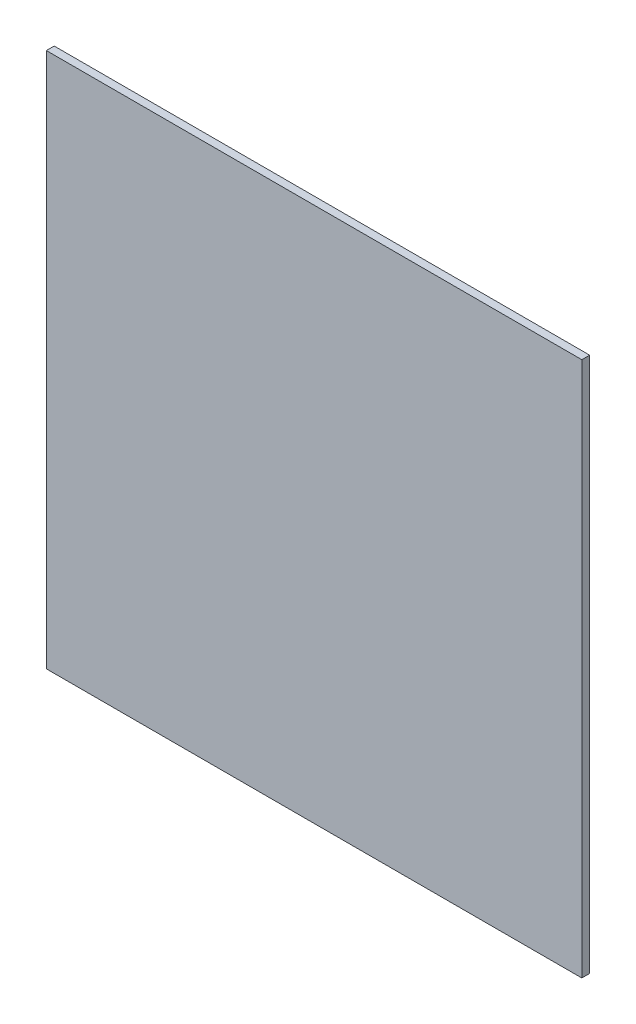
SolidWorks part; units mm, degrees
ref_plane "前视基准面" through (0, 0, 0) normal (0, 0, 1) x (1, 0, 0)
ref_plane "上视基准面" through (0, 0, 0) normal (0, 1, 0) x (1, 0, 0)
ref_plane "右视基准面" through (0, 0, 0) normal (1, 0, 0) x (0, 0, -1)
sketch "草图1" plane through (0, 0, 0) normal (0, 0, 1) x (1, 0, 0)
  line L1 (-25, 25) -> (50, 25)
  line L2 (-25, 25) -> (-25, -50)
  line L3 (-25, -50) -> (50, -50)
  line L4 (50, 25) -> (50, -50)
  circle A0 centre (0, 0) radius 25 construction
  dimension "D1" = 50
  dimension "D2" = 75
  dimension "D3" = 75
extrude "凸台-拉伸1" add sketch "草图1" along normal blind 1.1
